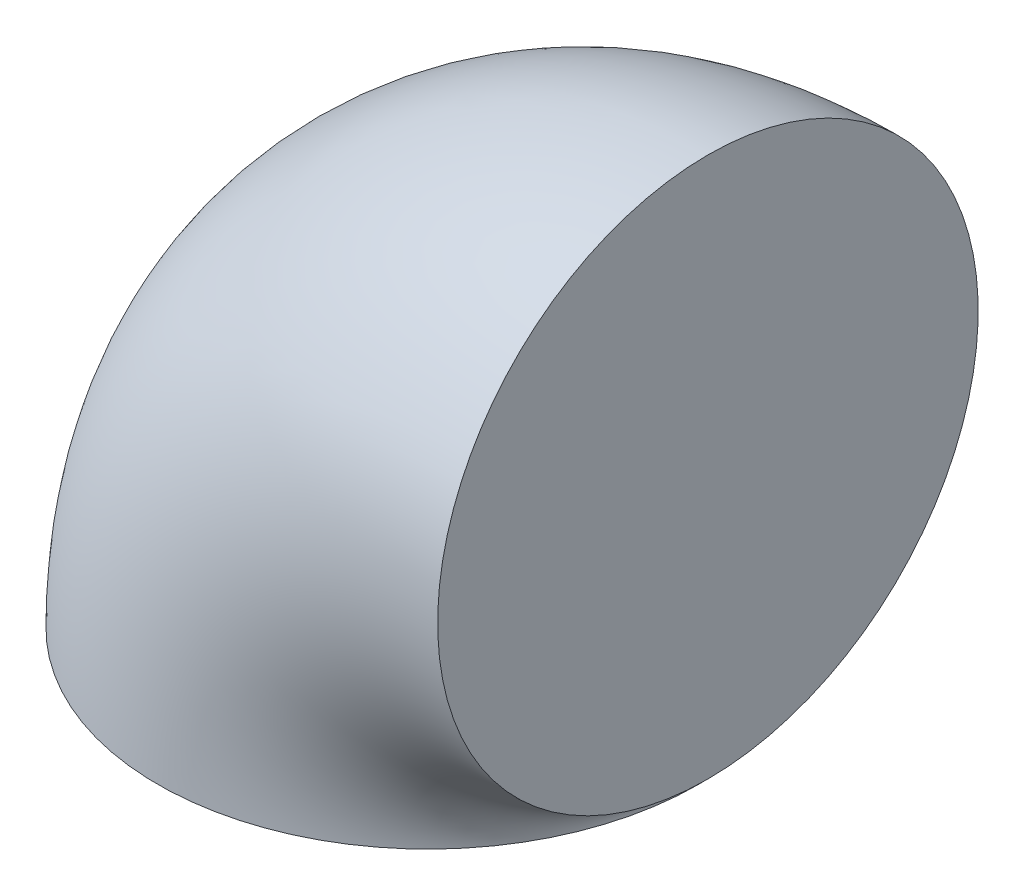
SolidWorks part; units mm, degrees
ref_plane "Plano frontal" through (0, 0, 0) normal (0, 0, 1) x (1, 0, 0)
ref_plane "Plano superior" through (0, 0, 0) normal (0, 1, 0) x (1, 0, 0)
ref_plane "Plano direito" through (0, 0, 0) normal (1, 0, 0) x (0, 0, -1)
sketch "Esboço1" plane through (0, 0, 0) normal (0, 1, 0) x (1, 0, 0)
  line L0 (0, 0) -> (64.7, 0)
  line L1 (64.7, 0) -> (64.7, 20)
  circle A0 centre (0, 0) radius 62.5
revolve "Revolução1" add sketch "Esboço1" angle 90 about L1
